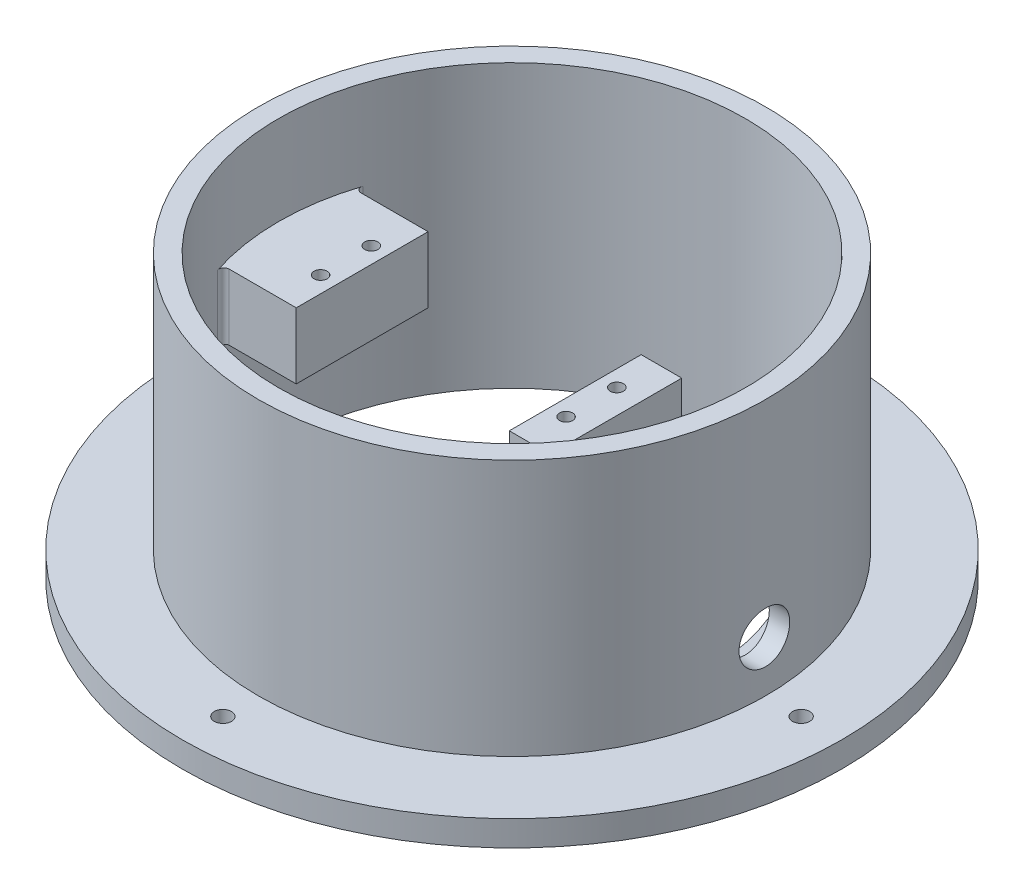
SolidWorks part; units mm, degrees
ref_plane "Front Plane" through (0, 0, 0) normal (0, 0, 1) x (1, 0, 0)
ref_plane "Top Plane" through (0, 0, 0) normal (0, 1, 0) x (1, 0, 0)
ref_plane "Right Plane" through (0, 0, 0) normal (1, 0, 0) x (0, 0, -1)
sketch "Sketch1" plane through (0, 0, 0) normal (0, 1, 0) x (1, 0, 0)
  circle A0 centre (0, 0) radius 65
  circle A1 centre (0, 0) radius 46
  circle A2 centre (0, -57) radius 1.7
  circle A3 centre (-57, 0) radius 1.7
  circle A4 centre (0, 57) radius 1.7
  circle A5 centre (57, 0) radius 1.7
  point P14 (0, 0)
  dimension "D1" = 130
  dimension "D2" = 92
  dimension "D3" = 3.4
  dimension "D4" = 57
  dimension "D5" = 4
extrude "Boss-Extrude1" add sketch "Sketch1" along normal blind 5
sketch "Sketch3" plane through (0, 5, 0) normal (0, 1, 0) x (1, 0, 0)
  circle A1 centre (0, 0) radius 50
  circle A2 centre (0, 0) radius 46 construction
  circle A3 centre (0, 0) radius 46
  dimension "D1" = 100
extrude "Boss-Extrude2" add sketch "Sketch3" along normal blind 50.6
sketch "Sketch4" plane through (0, 0, 0) normal (0, -1, 0) x (1, 0, 0)
  line L0 (30.9839, -34) -> (12.4636, -13)
  line L1 (12.4636, -13) -> (12.4636, 13)
  line L2 (12.4636, 13) -> (30.9839, 34)
  line L3 (24.4636, 16) -> (30.9839, 23.3933)
  line L4 (24.4636, 16) -> (24.4636, -16)
  line L5 (24.4636, -16) -> (30.9839, -23.3933)
  circle A0 centre (0, 0) radius 46 construction
  arc A1 (30.9839, -34) -> (30.9839, 34) centre (0, 0) ccw
  arc A2 (30.9839, -23.3933) -> (30.9839, 23.3933) centre (0, 0) ccw
  dimension "D1" = 68
  dimension "D2" = 26
  dimension "D3" = 13
  dimension "D4" = 28
  dimension "D5" = 12
  dimension "D6" = 32
extrude "Boss-Extrude3" add sketch "Sketch4" against normal blind 4
sketch "Sketch6" plane through (12.4636, 0, 0) normal (-1, 0, 0) x (0, 0, 1)
  line L0 (13, 4) -> (13, 38)
  line L1 (13, 38) -> (-13, 38)
  line L2 (-13, 38) -> (-13, 4)
  line L3 (-13, 4) -> (-5, 4)
  line L4 (-5, 4) -> (-5, 28)
  line L5 (-5, 28) -> (5, 28)
  line L6 (5, 28) -> (5, 4)
  line L7 (5, 4) -> (13, 4)
  dimension "D1" = 34
  dimension "D2" = 10
  dimension "D3" = 24
  dimension "D4" = 5
extrude "Boss-Extrude4" add sketch "Sketch6" against normal blind 8
sketch "Sketch7" plane through (0, 0, 0) normal (0, -1, 0) x (1, 0, 0)
  line L0 (-44.1248, 13) -> (12.4636, 13)
  line L1 (12.4636, 13) -> (12.4636, -13)
  line L2 (12.4636, -13) -> (-44.1248, -13)
  line L3 (12.4636, 13) -> (12.4636, -13) construction
  arc A0 (30.9839, 34) -> (30.9839, -34) centre (0, 0) ccw construction
  arc A1 (-44.1248, 13) -> (-44.1248, -13) centre (0, 0) ccw
  dimension "D1" = 26
  dimension "D3" = 13
extrude "Boss-Extrude5" add sketch "Sketch7" against normal up to surface (38 mm away) up to face at (16.4636, 38, 0)
ref_plane "Plane1" through (50, 0, 0) normal (1, 0, 0) x (0, 0, -1)
sketch "Sketch12" plane through (50, 0, 0) normal (1, 0, 0) x (0, 0, -1)
  line L0 (65, 5) -> (-65, 5) construction
  circle A0 centre (0, 15) radius 5
  dimension "D1" = 10
  dimension "D2" = 10
extrude "Cut-Extrude3" cut sketch "Sketch12" against normal up to surface (4.2725 mm away)
sketch "Sketch13" plane through (0, 38, 0) normal (0, 1, 0) x (1, 0, 0)
  line L0 (12.4636, 13) -> (12.4636, -13)
  line L1 (20.4636, 13) -> (-44.1248, 13) construction
  line L2 (20.4636, -13) -> (-44.1248, -13) construction
  line L3 (12.4636, -13) -> (-29.5364, -13)
  line L4 (-29.5364, -13) -> (-29.5364, 13)
  line L5 (-29.5364, 13) -> (12.4636, 13)
  dimension "D1" = 42
extrude "Cut-Extrude4" cut sketch "Sketch13" against normal up to surface (38 mm away) up to face at (-2.1644, 0, -26.9337)
sketch "Sketch14" plane through (0, 38, 0) normal (0, 1, 0) x (1, 0, 0)
  line L0 (12.4636, 0) -> (20.4636, 0) construction
  line L1 (12.4636, -13) -> (12.4636, 13) construction
  line L2 (20.4636, -13) -> (20.4636, 13) construction
  line L3 (-29.5364, 13) -> (-29.5364, -13) construction
  circle A0 centre (15.6636, 5) radius 1.3
  circle A1 centre (15.6636, -5) radius 1.3
  circle A2 centre (-32.7364, 5) radius 1.3
  circle A3 centre (-32.7364, -5) radius 1.3
  dimension "D1" = 2.6
  dimension "D2" = 10
  dimension "D3" = 2.6
  dimension "D4" = 3.2
  dimension "D5" = 3.2
extrude "Cut-Extrude5" cut sketch "Sketch14" against normal blind 7.5
sketch "Sketch15" plane through (0, 0, 0) normal (0, -1, 0) x (1, 0, 0)
  line L0 (-29.5364, 13) -> (-29.5364, -13) construction
  line L1 (-44.1248, 13) -> (-29.5364, 13)
  line L3 (-44.1248, -13) -> (-29.5364, -13)
  line L4 (-29.5364, 13) -> (-29.5364, -13)
  line L5 (-29.5364, 13) -> (-44.1248, 13) construction
  line L6 (-44.1248, -13) -> (-29.5364, -13) construction
  arc A0 (-44.1248, 13) -> (-44.1248, -13) centre (0, 0) ccw
  arc A1 (30.9839, 34) -> (-44.1248, 13) centre (0, 0) ccw construction
extrude "Cut-Extrude6" cut sketch "Sketch15" against normal offset from surface (25 mm away) 13 up to face at (-32.7364, 38, -3.7)
fillet "Fillet1" radius 1 9 edges at (-44.1248, 31.5, 13) (-44.1248, 31.5, -13) (-46, 25, 0) (16.4636, 4, 5) (16.4636, 4, -5) (16.4636, 4, -13) (16.4636, 4, 13) (20.4636, 4, 9) (20.4636, 4, -9)
